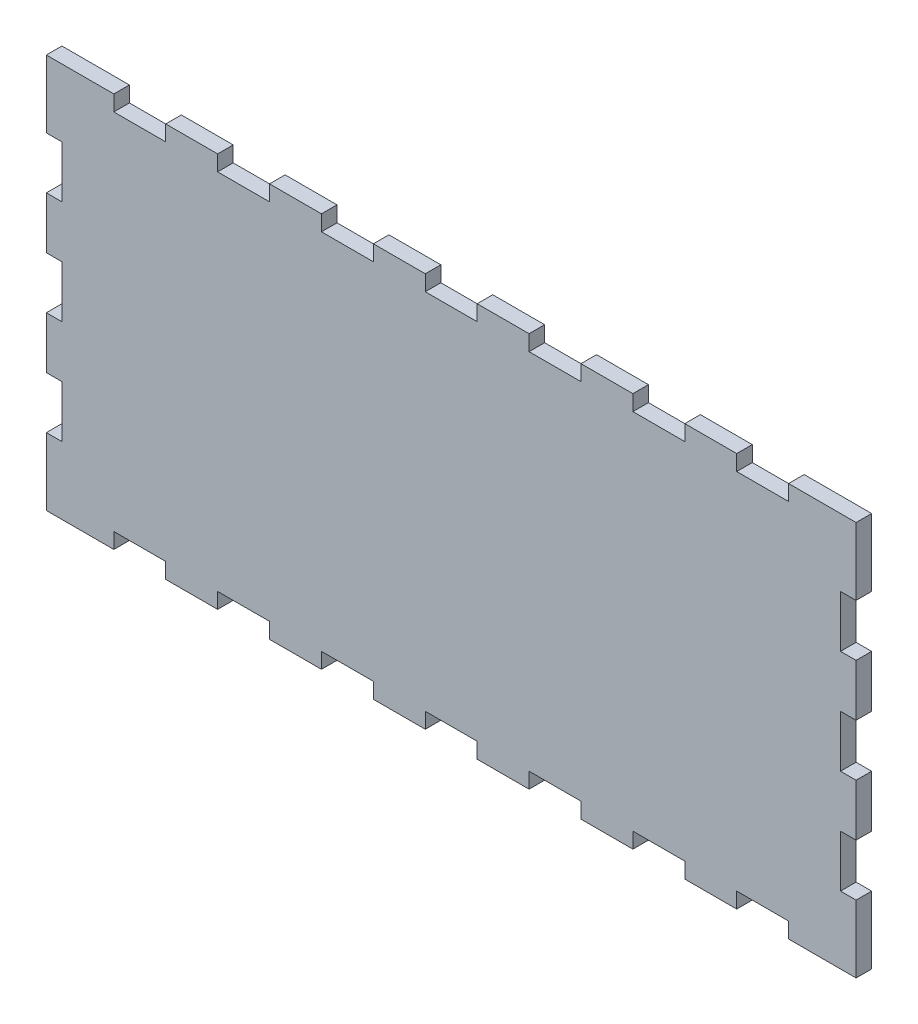
SolidWorks part; units mm, degrees
ref_plane "Front Plane" through (0, 0, 0) normal (0, 0, 1) x (1, 0, 0)
ref_plane "Top Plane" through (0, 0, 0) normal (0, 1, 0) x (1, 0, 0)
ref_plane "Right Plane" through (0, 0, 0) normal (1, 0, 0) x (0, 0, -1)
sketch "Sketch1" plane through (0, 0, 0) normal (0, 0, 1) x (1, 0, 0)
  line L2 (0, 60) -> (0, 50)
  line L4 (153, 73) -> (150, 73)
  line L5 (-3, 70) -> (-3, 60)
  line L6 (-3, 60) -> (0, 60)
  line L7 (0, 50) -> (-3, 50)
  line L8 (-3, 50) -> (-3, 40)
  line L9 (0, 40) -> (0, 30)
  line L10 (-3, 40) -> (0, 40)
  line L11 (0, 30) -> (-3, 30)
  line L12 (-3, 30) -> (-3, 20)
  line L13 (0, 20) -> (0, 10)
  line L14 (-3, 20) -> (0, 20)
  line L15 (0, 10) -> (-3, 10)
  line L16 (-3, 10) -> (-3, 0)
  line L18 (-3, 0) -> (0, 0)
  line L19 (0, 0) -> (0, -10) [skipped]
  line L20 (150, 20) -> (150, 10)
  line L21 (150, 40) -> (150, 30)
  line L22 (150, 60) -> (150, 50)
  line L24 (150, 10) -> (153, 10)
  line L25 (153, 20) -> (150, 20)
  line L26 (150, 30) -> (153, 30)
  line L27 (153, 40) -> (150, 40)
  line L28 (150, 50) -> (153, 50)
  line L29 (130, 73) -> (130, 70)
  line L30 (153, 60) -> (150, 60)
  line L31 (153, 10) -> (153, 0)
  line L32 (153, 30) -> (153, 20)
  line L33 (153, 50) -> (153, 40)
  line L34 (153, 70) -> (153, 60)
  line L35 (150, 73) -> (140, 73)
  line L36 (153, 70) -> (153, 73)
  line L37 (140, 73) -> (140, 70)
  line L38 (140, 70) -> (130, 70)
  line L39 (130, 73) -> (120, 73)
  line L40 (120, 70) -> (110, 70)
  line L41 (120, 73) -> (120, 70)
  line L42 (110, 73) -> (110, 70)
  line L43 (110, 73) -> (100, 73)
  line L44 (100, 70) -> (90, 70)
  line L45 (100, 73) -> (100, 70)
  line L46 (90, 73) -> (90, 70)
  line L47 (90, 73) -> (80, 73)
  line L48 (80, 70) -> (70, 70)
  line L49 (80, 73) -> (80, 70)
  line L50 (70, 73) -> (70, 70)
  line L51 (70, 73) -> (60, 73)
  line L52 (60, 70) -> (50, 70)
  line L53 (60, 73) -> (60, 70)
  line L54 (50, 73) -> (50, 70)
  line L55 (50, 73) -> (40, 73)
  line L56 (40, 70) -> (30, 70)
  line L57 (40, 73) -> (40, 70)
  line L58 (30, 73) -> (30, 70)
  line L59 (30, 73) -> (20, 73)
  line L60 (20, 70) -> (10, 70)
  line L61 (20, 73) -> (20, 70)
  line L62 (10, 70) -> (10, 73)
  line L63 (10, 73) -> (0, 73)
  line L64 (-3, -3) -> (-3, 0)
  line L65 (0, 73) -> (-3, 73)
  line L66 (-3, 73) -> (-3, 70)
  line L67 (0, -3) -> (-3, -3)
  line L68 (10, -3) -> (0, -3)
  line L69 (10, 0) -> (10, -3)
  line L70 (20, -3) -> (20, 0)
  line L71 (20, 0) -> (10, 0)
  line L72 (30, -3) -> (20, -3)
  line L73 (30, -3) -> (30, 0)
  line L74 (40, -3) -> (40, 0)
  line L75 (40, 0) -> (30, 0)
  line L76 (50, -3) -> (40, -3)
  line L77 (50, -3) -> (50, 0)
  line L78 (60, -3) -> (60, 0)
  line L79 (60, 0) -> (50, 0)
  line L80 (70, -3) -> (60, -3)
  line L81 (70, -3) -> (70, 0)
  line L82 (80, -3) -> (80, 0)
  line L83 (80, 0) -> (70, 0)
  line L84 (90, -3) -> (80, -3)
  line L85 (90, -3) -> (90, 0)
  line L86 (100, -3) -> (100, 0)
  line L87 (100, 0) -> (90, 0)
  line L88 (110, -3) -> (100, -3)
  line L89 (110, -3) -> (110, 0)
  line L90 (120, -3) -> (120, 0)
  line L91 (120, 0) -> (110, 0)
  line L92 (130, -3) -> (120, -3)
  line L93 (140, 0) -> (130, 0)
  line L94 (140, -3) -> (140, 0)
  line L95 (153, 0) -> (153, -3)
  line L96 (150, -3) -> (140, -3)
  line L97 (130, -3) -> (130, 0)
  line L98 (153, -3) -> (150, -3)
  dimension "D1" = 4
  dimension "D2" = 7
extrude "Boss-Extrude1" add sketch "Sketch1" along normal blind 3 contours L98 L95 L31 L24 L20 L25 L32 L26 L21 L27 L33 L28 L22 L30 L34 L36 L4 L35 L37 L38 L29 L39 L41 L40 L42 L43 L45 L44 L46 L47 L49 L48 L50 L51 L53 L52 L54 L55 L57 L56 L58 L59 L61 L60 L62 L63 L65 L66 L5 L6 L2
